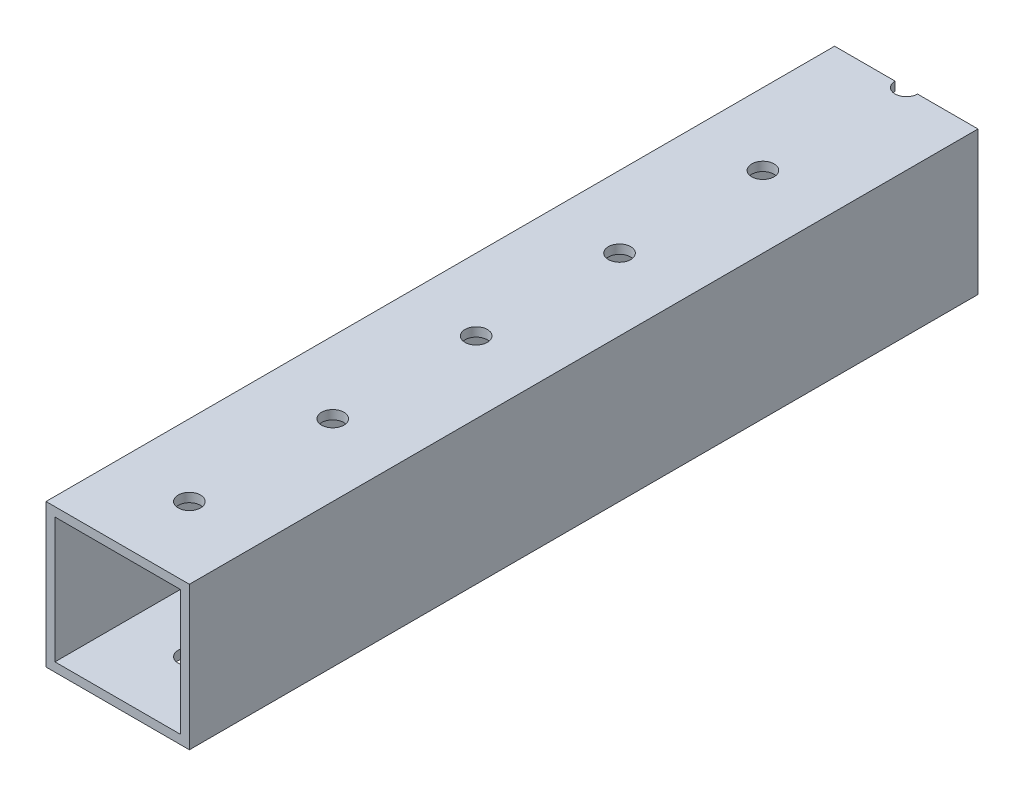
SolidWorks part; units mm, degrees
ref_plane "Front Plane" through (0, 0, 0) normal (0, 0, 1) x (1, 0, 0)
ref_plane "Top Plane" through (0, 0, 0) normal (0, 1, 0) x (1, 0, 0)
ref_plane "Right Plane" through (0, 0, 0) normal (1, 0, 0) x (0, 0, -1)
sketch "Sketch1" plane through (0, 0, 0) normal (0, 0, 1) x (1, 0, 0)
  line L1 (-11.1125, 11.1125) -> (11.1125, 11.1125)
  line L2 (-11.1125, 11.1125) -> (-11.1125, -11.1125)
  line L3 (-11.1125, -11.1125) -> (11.1125, -11.1125)
  line L4 (11.1125, 11.1125) -> (11.1125, -11.1125)
  line L5 (-11.1125, 11.1125) -> (11.1125, -11.1125) construction
  line L6 (-11.1125, -11.1125) -> (11.1125, 11.1125) construction
  line L7 (-12.7, 12.7) -> (12.7, 12.7)
  line L8 (-12.7, 12.7) -> (-12.7, -12.7)
  line L9 (-12.7, -12.7) -> (12.7, -12.7)
  line L10 (12.7, 12.7) -> (12.7, -12.7)
  line L11 (-12.7, 12.7) -> (12.7, -12.7) construction
  line L12 (-12.7, -12.7) -> (12.7, 12.7) construction
  point P0 (0, 0)
  point P6 (0, 0)
  dimension "D1" = 25.4
  dimension "D2" = 25.4
  dimension "D3" = 1.5875
extrude "Boss-Extrude1" add sketch "Sketch1" along normal blind 139.7
sketch "Sketch2" plane through (0, 12.7, 0) normal (0, 1, 0) x (1, 0, 0)
  line L0 (0, -139.7) -> (0, -127) construction
  line L1 (12.7, -139.7) -> (-12.7, -139.7) construction
  circle A0 centre (0, -127) radius 1.9844
  circle A1 centre (0, -101.6) radius 1.9844
  circle A2 centre (0, -76.2) radius 1.9844
  circle A3 centre (0, -50.8) radius 1.9844
  circle A4 centre (0, -25.4) radius 1.9844
  circle A5 centre (0, 0) radius 1.9844
  circle A6 centre (0, 25.4) radius 1.9844
  circle A7 centre (0, 50.8) radius 1.9844
  circle A8 centre (0, 76.2) radius 1.9844
  circle A9 centre (0, 101.6) radius 1.9844
  circle A10 centre (0, 127) radius 1.9844
  circle A11 centre (0, 152.4) radius 1.9844
  dimension "D2" = 3.9688
  dimension "D1" = 12.7
  dimension "D3" = 12
extrude "Cut-Extrude1" cut sketch "Sketch2" against normal through all
